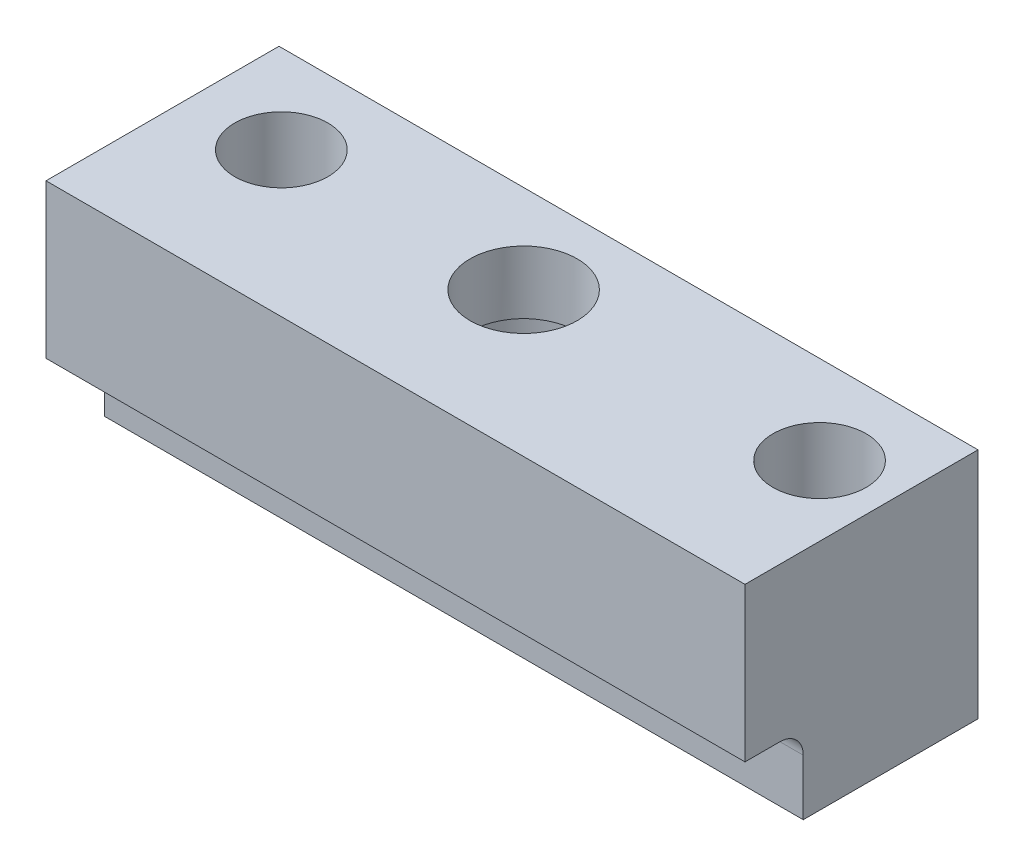
SolidWorks part; units mm, degrees
ref_plane "Front Plane" through (0, 0, 0) normal (0, 0, 1) x (1, 0, 0)
ref_plane "Top Plane" through (0, 0, 0) normal (0, 1, 0) x (1, 0, 0)
ref_plane "Right Plane" through (0, 0, 0) normal (1, 0, 0) x (0, 0, -1)
sketch "Sketch1" plane through (0, 0, 0) normal (1, 0, 0) x (0, 0, -1)
  line L0 (0, 0) -> (-6.35, 0)
  line L1 (-6.35, 0) -> (-6.35, 16.764)
  line L2 (-6.35, 16.764) -> (19.05, 16.764)
  line L3 (19.05, 16.764) -> (19.05, -8.636)
  line L4 (19.05, -8.636) -> (0, -8.636)
  line L5 (0, -8.636) -> (0, 0)
  dimension "D1" = 6.35
  dimension "D2" = 25.4
  dimension "D3" = 25.4
  dimension "D4" = 8.636
extrude "Boss-Extrude1" add sketch "Sketch1" along normal blind 39.878 and the other way blind 36.322
fillet "Fillet1" radius 2.54 1 edges at (1.778, 0, 0)
sketch "Sketch2" plane through (0, 16.764, 0) normal (0, 1, 0) x (1, 0, 0)
  line L0 (-36.322, 19.05) -> (-36.322, 9.398) construction
  line L1 (-36.322, 19.05) -> (-36.322, -6.35) construction
  line L2 (-36.322, 9.398) -> (-26.416, 9.398) construction
  line L3 (-26.416, 9.398) -> (0, 9.398) construction
  line L4 (0, 9.398) -> (32.258, 9.398) construction
  line L5 (32.258, 9.398) -> (39.878, 9.398) construction
  line L7 (39.878, 19.05) -> (39.878, -6.35) construction
  circle A0 centre (-26.416, 9.398) radius 5.08
  circle A1 centre (0, 9.398) radius 5.842
  circle A2 centre (32.258, 9.398) radius 5.08
  dimension "D1" = 10.16
  dimension "D2" = 11.684
  dimension "D3" = 10.16
  dimension "D6" = 36.322
  dimension "D4" = 9.906
  dimension "D5" = 9.652
  dimension "D8" = 7.62
extrude "Cut-Extrude1" cut sketch "Sketch2" against normal through all contours A0 | A2 | A1
sketch "Sketch3" plane through (0, -8.636, 0) normal (0, -1, 0) x (1, 0, 0)
  circle A0 centre (0, -9.398) radius 7.366
  dimension "D1" = 14.732
extrude "Cut-Extrude2" cut sketch "Sketch3" against normal blind 18.542
